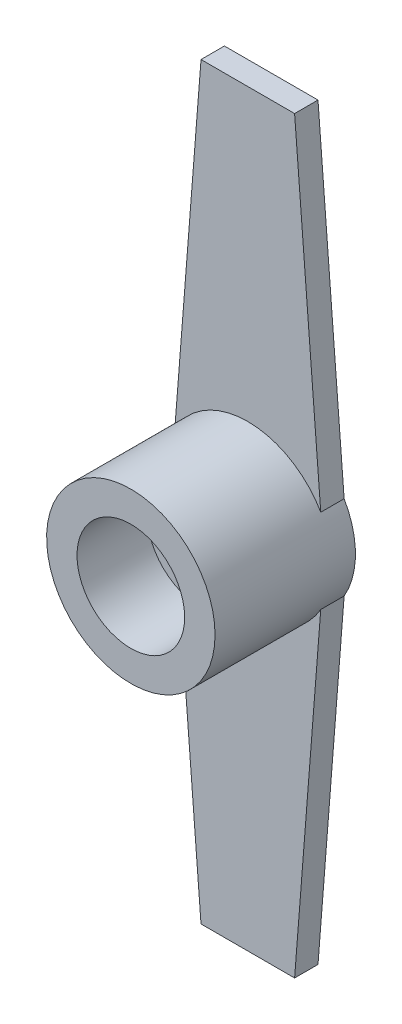
SolidWorks part; units mm, degrees
material "Resina de melamina"
ref_plane "Alzado" through (0, 0, 0) normal (0, 0, 1) x (1, 0, 0)
ref_plane "Planta" through (0, 0, 0) normal (0, 1, 0) x (1, 0, 0)
ref_plane "Vista lateral" through (0, 0, 0) normal (1, 0, 0) x (0, 0, -1)
sketch "Croquis1" plane through (0, 0, 0) normal (0, 0, 1) x (1, 0, 0)
  line L0 (0, 0) -> (0, -16) construction
  line L1 (-2, -16) -> (2, -16)
  line L2 (0, 0) -> (3.6, 0) construction
  line L3 (0, -3.6) -> (0, 0) construction
  line L4 (0, 0) -> (0, -1.8) construction
  line L5 (0, -1.8) -> (3.1177, -1.8) construction
  line L6 (3.1177, -1.8) -> (2, -16)
  line L7 (-2, 16) -> (2, 16)
  line L8 (3.1177, 1.8) -> (2, 16)
  line L9 (-3.1177, -1.8) -> (-2, -16)
  line L10 (-3.1177, 1.8) -> (-2, 16)
  circle A0 centre (0, 0) radius 3.6 construction
  arc A1 (3.1177, 1.8) -> (3.1177, -1.8) centre (0, 0) cw
  arc A2 (-3.1177, 1.8) -> (-3.1177, -1.8) centre (0, 0) ccw
  point P17 (0, 16)
extrude "Saliente-Extruir1" add sketch "Croquis1" along normal blind 1
sketch "Croquis2" plane through (0, 0, 1) normal (0, 0, 1) x (1, 0, 0)
  circle A0 centre (0, 0) radius 3.6
extrude "Saliente-Extruir2" add sketch "Croquis2" along normal blind 5
sketch "Croquis3" plane through (0, 0, 6) normal (0, 0, 1) x (1, 0, 0)
  circle A0 centre (0, 0) radius 2.3
extrude "Cortar-Extruir1" cut sketch "Croquis3" against normal blind 3 contours A0
